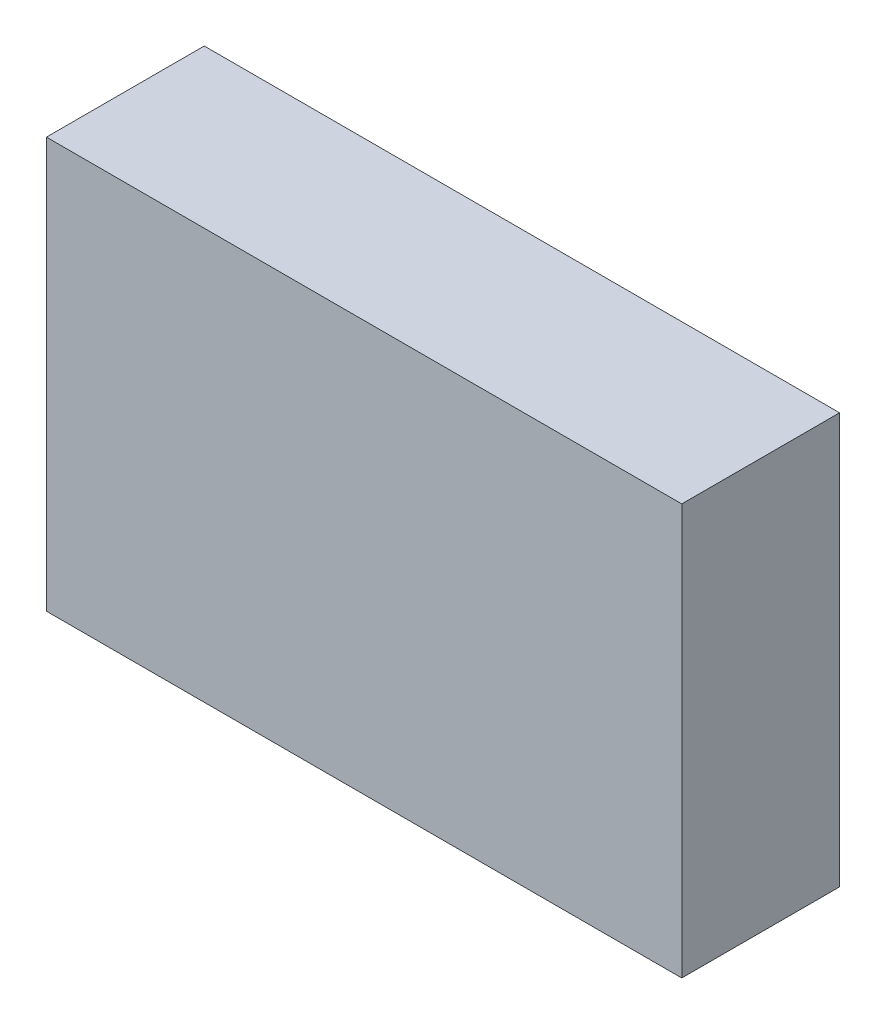
SolidWorks part; units mm, degrees
material "POM Acetal Copolymer"
ref_plane "Front Plane" through (0, 0, 0) normal (0, 0, 1) x (1, 0, 0)
ref_plane "Top Plane" through (0, 0, 0) normal (0, 1, 0) x (1, 0, 0)
ref_plane "Right Plane" through (0, 0, 0) normal (1, 0, 0) x (0, 0, -1)
sketch "Sketch1" plane through (0, 0, 0) normal (0, 0, 1) x (1, 0, 0)
  line L1 (31, -21.8727) -> (-31, -21.8727)
  line L2 (31, -21.8727) -> (31, 18.1959)
  line L3 (31, 18.1959) -> (-31, 18.1959)
  line L4 (-31, -21.8727) -> (-31, 18.1959)
  line L5 (31, -21.8727) -> (-31, 18.1959) construction
  line L6 (31, 18.1959) -> (-31, -21.8727) construction
  point P0 (0, 0)
  dimension "D2" = 62
extrude "Boss-Extrude1" add sketch "Sketch1" along normal blind 15.4
